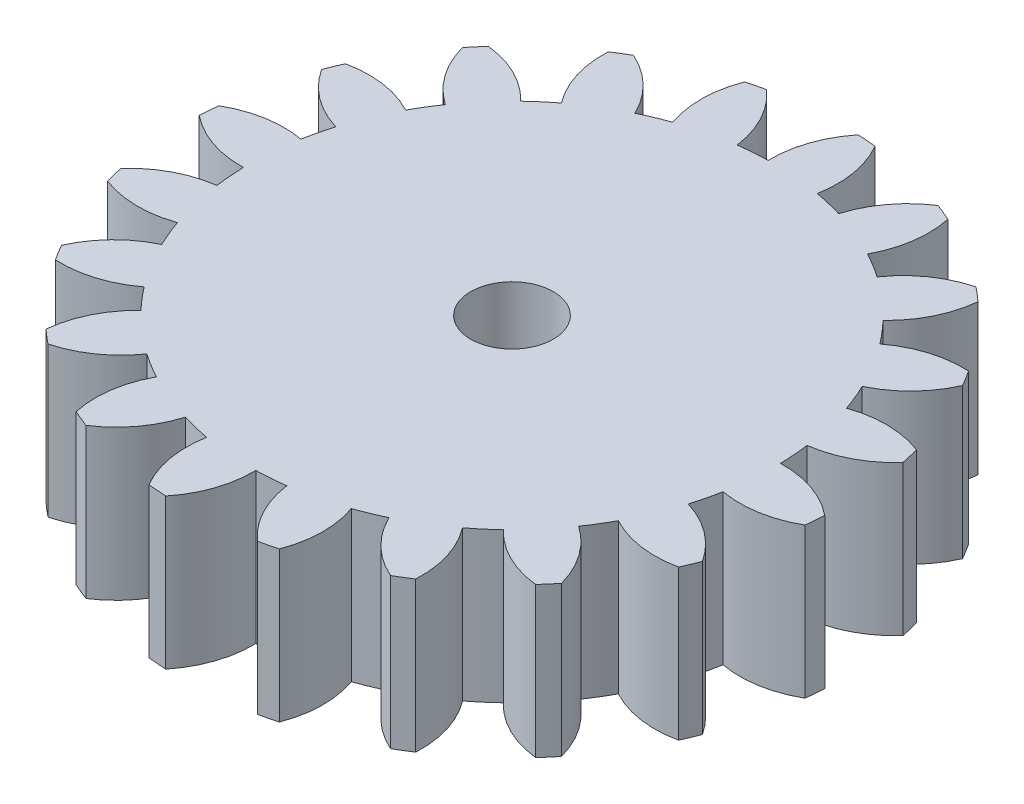
SolidWorks part; units mm, degrees
ref_plane "前视基准面" through (0, 0, 0) normal (0, 0, 1) x (1, 0, 0)
ref_plane "上视基准面" through (0, 0, 0) normal (0, 1, 0) x (1, 0, 0)
ref_plane "右视基准面" through (0, 0, 0) normal (1, 0, 0) x (0, 0, -1)
sketch "草图1" plane through (0, 0, 0) normal (0, 1, 0) x (1, 0, 0)
  line L0 (0, 0) -> (0, 22) construction
  line L1 (0, 0) -> (10.9643, 30.1242) construction
  line L2 (0, 0) -> (2.8303, 35.9623) construction
  line L3 (0, 20) -> (6.4279, 17.6604) construction
  line L4 (-2.3314, 17.344) -> (-5.7967, 16.512) construction
  line L5 (-3.5509, 22.3812) -> (0.006, 22.6612) construction
  line L6 (-2.0211, 17.9054) -> (-0.8048, 18.0012) construction
  line L7 (-1.413, 17.9533) -> (-1.7725, 22.5212) construction
  line L8 (-1.373, 17.4461) -> (1.6374, 17.683) construction
  line L9 (2.7127, 22.8742) -> (6.2696, 23.1541) construction
  line L10 (4.2426, 18.3984) -> (5.4588, 18.4941) construction
  line L11 (4.4912, 23.0141) -> (4.8507, 18.4463) construction
  circle A0 centre (0, 0) radius 22 construction
  circle A1 centre (0, 0) radius 17.5 construction
  circle A2 centre (0, 0) radius 20 construction
  circle A3 centre (6.4279, 17.6604) radius 6.8404 construction
  arc A4 (1.1171, 21.9716) -> (-0.4105, 17.4952) centre (6.4279, 17.6604) ccw
  arc A5 (2.3338, 21.8759) -> (3.1423, 17.2156) centre (-3.586, 18.4486) cw
  arc A6 (1.1171, 21.9716) -> (2.3338, 21.8759) centre (0, 0) cw
  arc A7 (7.852, 20.5511) -> (5.0159, 16.7658) centre (11.5707, 14.8098) ccw
  arc A8 (7.852, 20.5511) -> (8.9796, 20.084) centre (0, 0) cw
  arc A9 (8.9796, 20.084) -> (8.3084, 15.4019) centre (2.2904, 18.6538) cw
  arc A10 (13.8183, 17.1188) -> (9.9513, 14.3952) centre (15.5808, 10.5094) ccw
  arc A11 (13.8183, 17.1188) -> (14.7464, 16.3262) centre (0, 0) cw
  arc A12 (14.7464, 16.3262) -> (12.6613, 12.0807) centre (7.9426, 17.033) cw
  arc A13 (18.432, 12.0109) -> (13.9126, 10.6155) centre (18.0658, 5.1803) ccw
  arc A14 (18.432, 12.0109) -> (19.0697, 10.9702) centre (0, 0) cw
  arc A15 (19.0697, 10.9702) -> (15.7747, 7.5769) centre (12.8174, 13.745) cw
  arc A16 (21.2414, 5.7272) -> (16.512, 5.7967) centre (18.7824, -0.6559) ccw
  arc A17 (21.2414, 5.7272) -> (21.5264, 4.5404) centre (0, 0) cw
  arc A18 (21.5264, 4.5404) -> (17.344, 2.3314) centre (16.4375, 9.1114) cw
  arc A19 (21.9716, -1.1171) -> (17.4952, 0.4105) centre (17.6604, -6.4279) ccw
  arc A20 (21.9716, -1.1171) -> (21.8759, -2.3338) centre (0, 0) cw
  arc A21 (21.8759, -2.3338) -> (17.2156, -3.1423) centre (18.4486, 3.586) cw
  arc A22 (20.5511, -7.852) -> (16.7658, -5.0159) centre (14.8098, -11.5707) ccw
  arc A23 (20.5511, -7.852) -> (20.084, -8.9796) centre (0, 0) cw
  arc A24 (20.084, -8.9796) -> (15.4019, -8.3084) centre (18.6538, -2.2904) cw
  arc A25 (17.1188, -13.8183) -> (14.3952, -9.9513) centre (10.5094, -15.5808) ccw
  arc A26 (17.1188, -13.8183) -> (16.3262, -14.7464) centre (0, 0) cw
  arc A27 (16.3262, -14.7464) -> (12.0807, -12.6613) centre (17.033, -7.9426) cw
  arc A28 (12.0109, -18.432) -> (10.6155, -13.9126) centre (5.1803, -18.0658) ccw
  arc A29 (12.0109, -18.432) -> (10.9702, -19.0697) centre (0, 0) cw
  arc A30 (10.9702, -19.0697) -> (7.5769, -15.7747) centre (13.745, -12.8174) cw
  arc A31 (5.7272, -21.2414) -> (5.7967, -16.512) centre (-0.6559, -18.7824) ccw
  arc A32 (5.7272, -21.2414) -> (4.5404, -21.5264) centre (0, 0) cw
  arc A33 (4.5404, -21.5264) -> (2.3314, -17.344) centre (9.1114, -16.4375) cw
  arc A34 (-1.1171, -21.9716) -> (0.4105, -17.4952) centre (-6.4279, -17.6604) ccw
  arc A35 (-1.1171, -21.9716) -> (-2.3338, -21.8759) centre (0, 0) cw
  arc A36 (-2.3338, -21.8759) -> (-3.1423, -17.2156) centre (3.586, -18.4486) cw
  arc A37 (-7.852, -20.5511) -> (-5.0159, -16.7658) centre (-11.5707, -14.8098) ccw
  arc A38 (-7.852, -20.5511) -> (-8.9796, -20.084) centre (0, 0) cw
  arc A39 (-8.9796, -20.084) -> (-8.3084, -15.4019) centre (-2.2904, -18.6538) cw
  arc A40 (-13.8183, -17.1188) -> (-9.9513, -14.3952) centre (-15.5808, -10.5094) ccw
  arc A41 (-13.8183, -17.1188) -> (-14.7464, -16.3262) centre (0, 0) cw
  arc A42 (-14.7464, -16.3262) -> (-12.6613, -12.0807) centre (-7.9426, -17.033) cw
  arc A43 (-18.432, -12.0109) -> (-13.9126, -10.6155) centre (-18.0658, -5.1803) ccw
  arc A44 (-18.432, -12.0109) -> (-19.0697, -10.9702) centre (0, 0) cw
  arc A45 (-19.0697, -10.9702) -> (-15.7747, -7.5769) centre (-12.8174, -13.745) cw
  arc A46 (-21.2414, -5.7272) -> (-16.512, -5.7967) centre (-18.7824, 0.6559) ccw
  arc A47 (-21.2414, -5.7272) -> (-21.5264, -4.5404) centre (0, 0) cw
  arc A48 (-21.5264, -4.5404) -> (-17.344, -2.3314) centre (-16.4375, -9.1114) cw
  arc A49 (-21.9716, 1.1171) -> (-17.4952, -0.4105) centre (-17.6604, 6.4279) ccw
  arc A50 (-21.9716, 1.1171) -> (-21.8759, 2.3338) centre (0, 0) cw
  arc A51 (-21.8759, 2.3338) -> (-17.2156, 3.1423) centre (-18.4486, -3.586) cw
  arc A52 (-20.5511, 7.852) -> (-16.7658, 5.0159) centre (-14.8098, 11.5707) ccw
  arc A53 (-20.5511, 7.852) -> (-20.084, 8.9796) centre (0, 0) cw
  arc A54 (-20.084, 8.9796) -> (-15.4019, 8.3084) centre (-18.6538, 2.2904) cw
  arc A55 (-17.1188, 13.8183) -> (-14.3952, 9.9513) centre (-10.5094, 15.5808) ccw
  arc A56 (-17.1188, 13.8183) -> (-16.3262, 14.7464) centre (0, 0) cw
  arc A57 (-16.3262, 14.7464) -> (-12.0807, 12.6613) centre (-17.033, 7.9426) cw
  arc A58 (-12.0109, 18.432) -> (-10.6155, 13.9126) centre (-5.1803, 18.0658) ccw
  arc A59 (-12.0109, 18.432) -> (-10.9702, 19.0697) centre (0, 0) cw
  arc A60 (-10.9702, 19.0697) -> (-7.5769, 15.7747) centre (-13.745, 12.8174) cw
  arc A61 (-5.7272, 21.2414) -> (-5.7967, 16.512) centre (0.6559, 18.7824) ccw
  arc A62 (-5.7272, 21.2414) -> (-4.5404, 21.5264) centre (0, 0) cw
  arc A63 (-4.5404, 21.5264) -> (-2.3314, 17.344) centre (-9.1114, 16.4375) cw
  arc A64 (-2.3314, 17.344) -> (-0.4105, 17.4952) centre (0, 0) cw
  arc A65 (3.1423, 17.2156) -> (5.0159, 16.7658) centre (0, 0) cw
  arc A66 (8.3084, 15.4019) -> (9.9513, 14.3952) centre (0, 0) cw
  arc A67 (12.6613, 12.0807) -> (13.9126, 10.6155) centre (0, 0) cw
  arc A68 (15.7747, 7.5769) -> (16.512, 5.7967) centre (0, 0) cw
  arc A69 (17.344, 2.3314) -> (17.4952, 0.4105) centre (0, 0) cw
  arc A70 (17.2156, -3.1423) -> (16.7658, -5.0159) centre (0, 0) cw
  arc A71 (15.4019, -8.3084) -> (14.3952, -9.9513) centre (0, 0) cw
  arc A72 (12.0807, -12.6613) -> (10.6155, -13.9126) centre (0, 0) cw
  arc A73 (7.5769, -15.7747) -> (5.7967, -16.512) centre (0, 0) cw
  arc A74 (2.3314, -17.344) -> (0.4105, -17.4952) centre (0, 0) cw
  arc A75 (-3.1423, -17.2156) -> (-5.0159, -16.7658) centre (0, 0) cw
  arc A76 (-8.3084, -15.4019) -> (-9.9513, -14.3952) centre (0, 0) cw
  arc A77 (-12.6613, -12.0807) -> (-13.9126, -10.6155) centre (0, 0) cw
  arc A78 (-15.7747, -7.5769) -> (-16.512, -5.7967) centre (0, 0) cw
  arc A79 (-17.344, -2.3314) -> (-17.4952, -0.4105) centre (0, 0) cw
  arc A80 (-17.2156, 3.1423) -> (-16.7658, 5.0159) centre (0, 0) cw
  arc A81 (-15.4019, 8.3084) -> (-14.3952, 9.9513) centre (0, 0) cw
  arc A82 (-12.0807, 12.6613) -> (-10.6155, 13.9126) centre (0, 0) cw
  arc A83 (-7.5769, 15.7747) -> (-5.7967, 16.512) centre (0, 0) cw
  arc A84 (0.006, 22.6612) -> (-0.8048, 18.0012) centre (-6.7225, 21.4314) cw construction
  arc A85 (-2.0211, 17.9054) -> (-3.5509, 22.3812) centre (3.2872, 22.2192) cw construction
  arc A86 (6.2696, 23.1541) -> (5.4588, 18.4941) centre (-0.4589, 21.9243) cw construction
  arc A87 (4.2426, 18.3984) -> (2.7127, 22.8742) centre (9.5508, 22.7121) cw construction
  point P134 (0, 0)
  point P150 (-1.5394, 19.5599)
  point P162 (-1.5692, 19.9383)
  point P174 (0, 0)
  dimension "D1" = 40
  dimension "D2" = 44
  dimension "D3" = 35
  dimension "D8" = 4.5825
  dimension "D13" = 6.84
  dimension "D4" = 20
  dimension "D5" = 4.5
  dimension "D9" = 1.2205
  dimension "D10" = 1.22
  dimension "D11" = 4.582
  dimension "D12" = 4.73
  dimension "D14" = 1.22
  dimension "D15" = 4.582
  dimension "D16" = 2.5908
  dimension "D17" = 6.283
  dimension "D6" = 20
  dimension "D7" = 20
extrude "凸台-拉伸1" add sketch "草图1" along normal blind 10 contours A83 A60 A59 A58 A82 A57 A56 A55 A81 A54 A53 A52 A80 A51 A50 A49 A79 A48 A47 A46 A78 A45 A44 A43 A77 A42 A41 A40 A76 A39 A38 A37 A75 A36 A35 A34 A74 A33 A32 A31 A73 A30 A29 A28 A72 A27 A26 A25 A71 A24 A23
sketch "草图2" plane through (0, 10, 0) normal (0, 1, 0) x (1, 0, 0)
  circle A0 centre (0, 0) radius 2.7524
extrude "切除-拉伸1" cut sketch "草图2" against normal through all both and the other way through all
